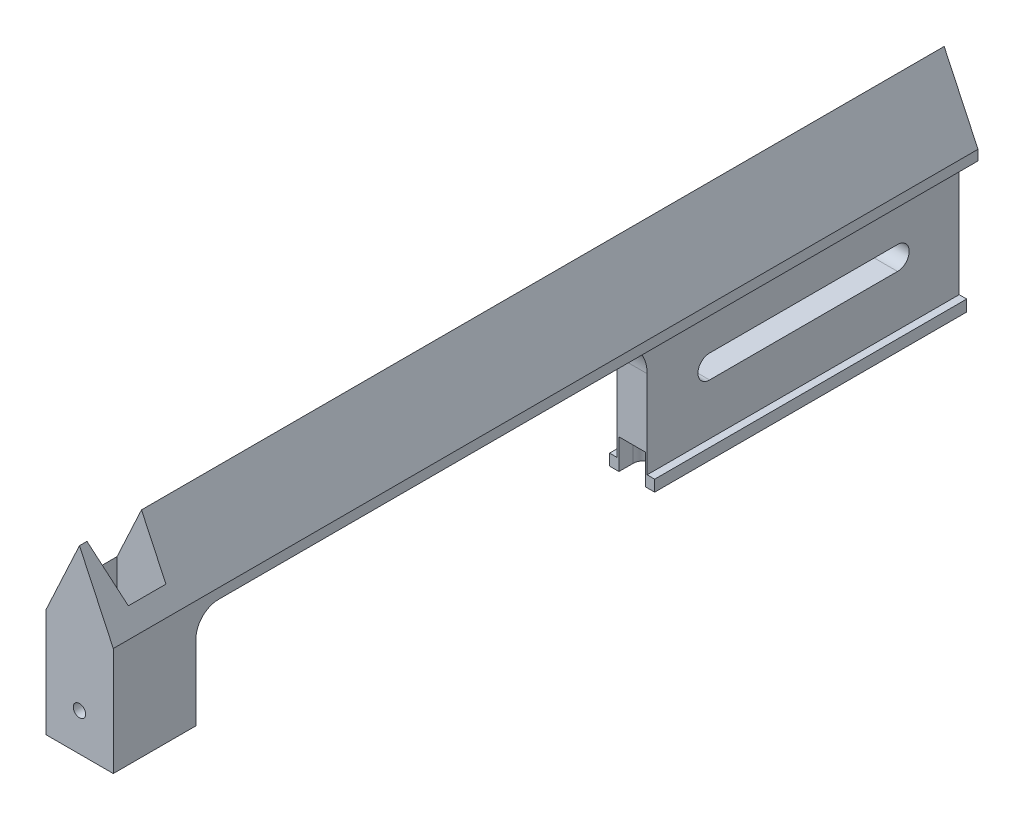
SolidWorks part; units mm, degrees
ref_plane "Front Plane" through (0, 0, 0) normal (0, 0, 1) x (1, 0, 0)
ref_plane "Top Plane" through (0, 0, 0) normal (0, 1, 0) x (1, 0, 0)
ref_plane "Right Plane" through (0, 0, 0) normal (1, 0, 0) x (0, 0, -1)
sketch "Sketch1" plane through (0, 0, 0) normal (0, 0, 1) x (1, 0, 0)
  line L0 (0, 0) -> (-8.9005, -19.1932)
  line L1 (-8.9005, -19.1932) -> (-8.9005, -58.18)
  line L2 (-8.9005, -58.18) -> (8.9995, -58.18)
  line L3 (8.9995, -58.18) -> (8.9995, -19.1932)
  line L4 (8.9995, -19.1932) -> (0, 0)
  line L5 (0, 48.1426) -> (0, -89.5342) construction
  dimension "D1" = 58.18
  dimension "D3" = 17.9
  dimension "D4" = 50
extrude "Boss-Extrude1" add sketch "Sketch1" along normal blind 230
sketch "Sketch3" plane through (0, 0, 0) normal (0, 0, -1) x (-1, 0, 0)
  line L0 (0, 3.1241) -> (0, -62.3933) construction
  line L1 (-6, -58.18) -> (-6, -55.18)
  line L2 (8.9005, -58.18) -> (-8.9995, -58.18) construction
  line L3 (-6, -55.18) -> (-4, -55.18)
  line L4 (-4, -55.18) -> (-4, -21.88)
  line L6 (-4, -21.88) -> (-8.9995, -21.88)
  line L7 (-8.9995, -21.88) -> (-8.9995, -58.18)
  line L8 (-8.9995, -58.18) -> (-6, -58.18)
  line L9 (6, -55.18) -> (4, -55.18)
  line L10 (6, -58.18) -> (6, -55.18)
  line L11 (8.9995, -58.18) -> (6, -58.18)
  line L12 (8.9995, -21.88) -> (8.9995, -58.18)
  line L13 (4, -21.88) -> (8.9995, -21.88)
  line L14 (4, -55.18) -> (4, -21.88)
  point P11 (-5, -55.18)
  dimension "D1" = 3
  dimension "D2" = 8
  dimension "D3" = 6
  dimension "D4" = 33.3
extrude "Cut-Extrude2" cut sketch "Sketch3" against normal blind 93 contours L9 L14 L13 L12 L11 L10 | L1 L3 L4 L6 L7 L8
sketch "Sketch4" plane through (-8.9005, 0, 0) normal (-1, 0, 0) x (0, 0, 1)
  line L0 (83, -58.18) -> (83, -21.88)
  line L1 (93, -58.18) -> (0, -58.18) construction
  line L2 (93, -21.88) -> (0, -21.88) construction
  line L3 (83, -21.88) -> (208, -21.88)
  line L4 (208, -21.88) -> (208, -58.18)
  line L5 (230, -58.18) -> (93, -58.18) construction
  line L6 (208, -58.18) -> (83, -58.18)
  line L7 (230, -19.1932) -> (230, -58.18) construction
  dimension "D1" = 22
  dimension "D2" = 125
  dimension "D3" = 36.3
extrude "Cut-Extrude3" cut sketch "Sketch4" against normal through all
fillet "Fillet3" radius 10 1 edges at (0, -21.88, 83)
fillet "Fillet4" radius 6 1 edges at (0.0495, -21.88, 208)
sketch "Sketch5" plane through (8.9995, 0, 0) normal (1, 0, 0) x (0, 0, -1)
  line L0 (-208, -58.18) -> (-208, -27.88) construction
  line L1 (-230, -58.18) -> (-208, -58.18)
  line L2 (-230, -58.18) -> (-230, -48)
  line L3 (-230, -48) -> (-208, -48)
  line L4 (-208, -58.18) -> (-208, -48)
  line L5 (-230, 0) -> (0, 0) construction
  dimension "D1" = 48
extrude "Cut-Extrude4" cut sketch "Sketch5" against normal through all
sketch "Sketch6" plane through (4, 0, 0) normal (1, 0, 0) x (0, 0, -1)
  line L0 (-66.4, -38.53) -> (-16.4, -38.53) construction
  line L1 (-66.4, -35.43) -> (-16.4, -35.43)
  line L2 (-66.4, -41.63) -> (-16.4, -41.63)
  line L3 (0, -55.18) -> (0, -21.88) construction
  line L5 (-83, -55.18) -> (0, -55.18) construction
  arc A0 (-66.4, -35.43) -> (-66.4, -41.63) centre (-66.4, -38.53) ccw
  arc A1 (-16.4, -41.63) -> (-16.4, -35.43) centre (-16.4, -38.53) ccw
  point P2 (-41.4, -38.53)
  point P7 (-41.4, -41.63)
  dimension "D1" = 6.2
  dimension "D2" = 50
  dimension "D3" = 16.4
  dimension "D4" = 16.65
extrude "Cut-Extrude5" cut sketch "Sketch6" against normal up to next
sketch "Sketch7" plane through (0, 0, 230) normal (0, 0, 1) x (1, 0, 0)
  line L0 (-8.9005, -48) -> (8.9995, -48) construction
  circle A0 centre (0, -38) radius 1.65
  dimension "D1" = 3.3
  dimension "D2" = 10
extrude "Cut-Extrude6" cut sketch "Sketch7" against normal up to next
sketch "Sketch8" plane through (0, -48, 0) normal (0, -1, 0) x (1, 0, 0)
  line L0 (0, 241.5442) -> (0, 176.9169) construction
  line L1 (0, 228) -> (-6.5, 223.5)
  line L2 (-6.5, 223.5) -> (-6.5, 213.5)
  line L3 (-6.5, 213.5) -> (6.5, 213.5)
  line L4 (-8.9005, 208) -> (8.9995, 208) construction
  line L5 (-8.9005, 208) -> (8.9995, 208) construction
  line L6 (6.5, 223.5) -> (6.5, 213.5)
  line L7 (0, 228) -> (6.5, 223.5)
  point P12 (0, 213.5)
  dimension "D1" = 13
  dimension "D2" = 10
  dimension "D3" = 5.5
  dimension "D4" = 20
extrude "Cut-Extrude7" cut sketch "Sketch8" against normal through all
sketch "Sketch9" plane through (0, -58.18, 0) normal (0, -1, 0) x (1, 0, 0)
  line L0 (0, -9.7639) -> (0, 107.2985) construction
  line L2 (-1.5, -19.0057) -> (1.5, -19.0057)
  line L3 (-1.5, -19.0057) -> (-1.5, 110.3791)
  line L4 (-1.5, 110.3791) -> (1.5, 110.3791)
  line L5 (1.5, -19.0057) -> (1.5, 110.3791)
  line L6 (-1.5, -19.0057) -> (1.5, 110.3791) construction
  line L7 (-1.5, 110.3791) -> (1.5, -19.0057) construction
  point P3 (0, 45.6867)
  dimension "D1" = 3
extrude "Cut-Extrude8" cut sketch "Sketch9" against normal blind 5 and the other way through all
sketch "Sketch10" plane through (0, -58.18, 0) normal (0, -1, 0) x (1, 0, 0)
  line L0 (4, 83) -> (-4, 83) construction
  line L1 (-3.5, 89.723) -> (3.5, 89.723)
  line L2 (-3.5, 89.723) -> (-3.5, 76.277)
  line L3 (-3.5, 76.277) -> (3.5, 76.277)
  line L4 (3.5, 89.723) -> (3.5, 76.277)
  line L5 (-3.5, 89.723) -> (3.5, 76.277) construction
  line L6 (-3.5, 76.277) -> (3.5, 89.723) construction
  point P0 (0, 83)
  dimension "D1" = 7
extrude "Cut-Extrude9" cut sketch "Sketch10" against normal blind 8
fillet "Fillet5" radius 3 2 edges at (3.5, -54.18, 76.277) (-3.5, -54.18, 76.277)
